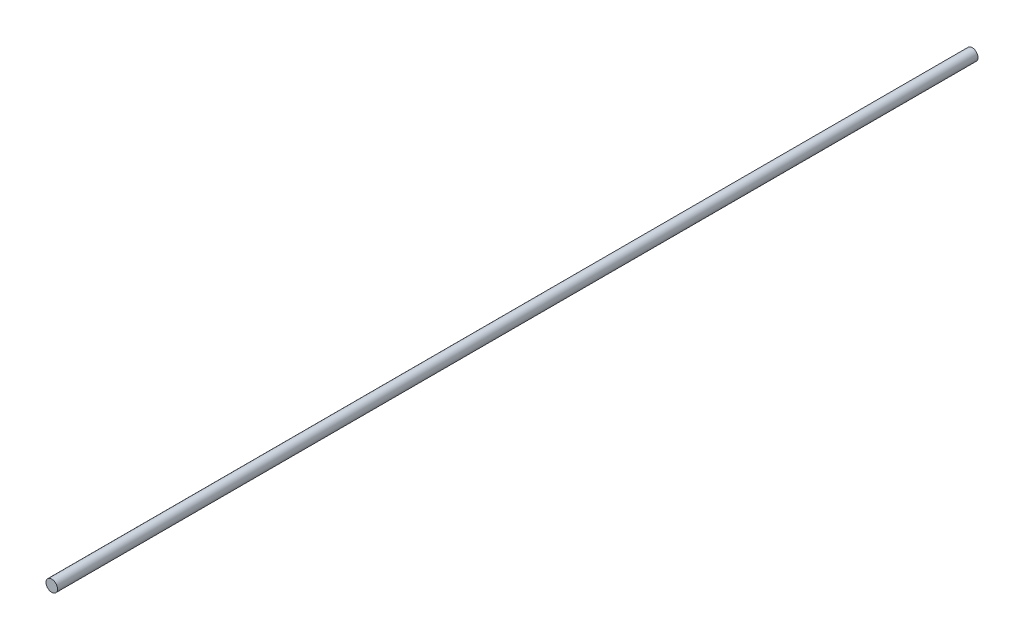
SolidWorks part; units mm, degrees
material "6061 Alloy"
ref_plane "Front Plane" through (0, 0, 0) normal (0, 0, 1) x (1, 0, 0)
ref_plane "Top Plane" through (0, 0, 0) normal (0, 1, 0) x (1, 0, 0)
ref_plane "Right Plane" through (0, 0, 0) normal (1, 0, 0) x (0, 0, -1)
sketch "Sketch1" plane through (0, 0, 0) normal (0, 0, 1) x (1, 0, 0)
  circle A0 centre (0, 0) radius 3.175
  dimension "D1" = 6.35
extrude "Boss-Extrude1" add sketch "Sketch1" along normal blind 508
